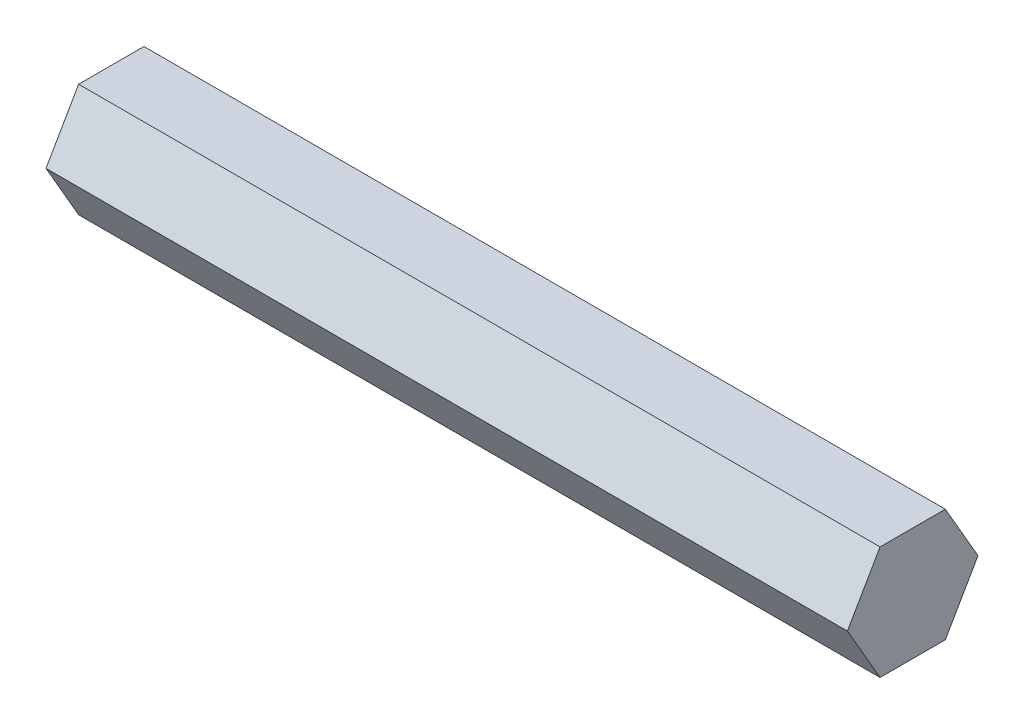
SolidWorks part; units mm, degrees
ref_plane "Front Plane" through (0, 0, 0) normal (0, 0, 1) x (1, 0, 0)
ref_plane "Top Plane" through (0, 0, 0) normal (0, 1, 0) x (1, 0, 0)
ref_plane "Right Plane" through (0, 0, 0) normal (1, 0, 0) x (0, 0, -1)
sketch "Sketch1" plane through (0, 0, 0) normal (1, 0, 0) x (0, 0, -1)
  line L1 (7.3323, 0) -> (3.6662, 6.35)
  line L2 (3.6662, 6.35) -> (-3.6662, 6.35)
  line L3 (-3.6662, 6.35) -> (-7.3323, 0)
  line L4 (-7.3323, 0) -> (-3.6662, -6.35)
  line L5 (-3.6662, -6.35) -> (3.6662, -6.35)
  line L6 (3.6662, -6.35) -> (7.3323, 0)
  circle A0 centre (0, 0) radius 6.35 construction
  dimension "D1" = 12.7
extrude "Boss-Extrude1" add sketch "Sketch1" along normal blind 90
